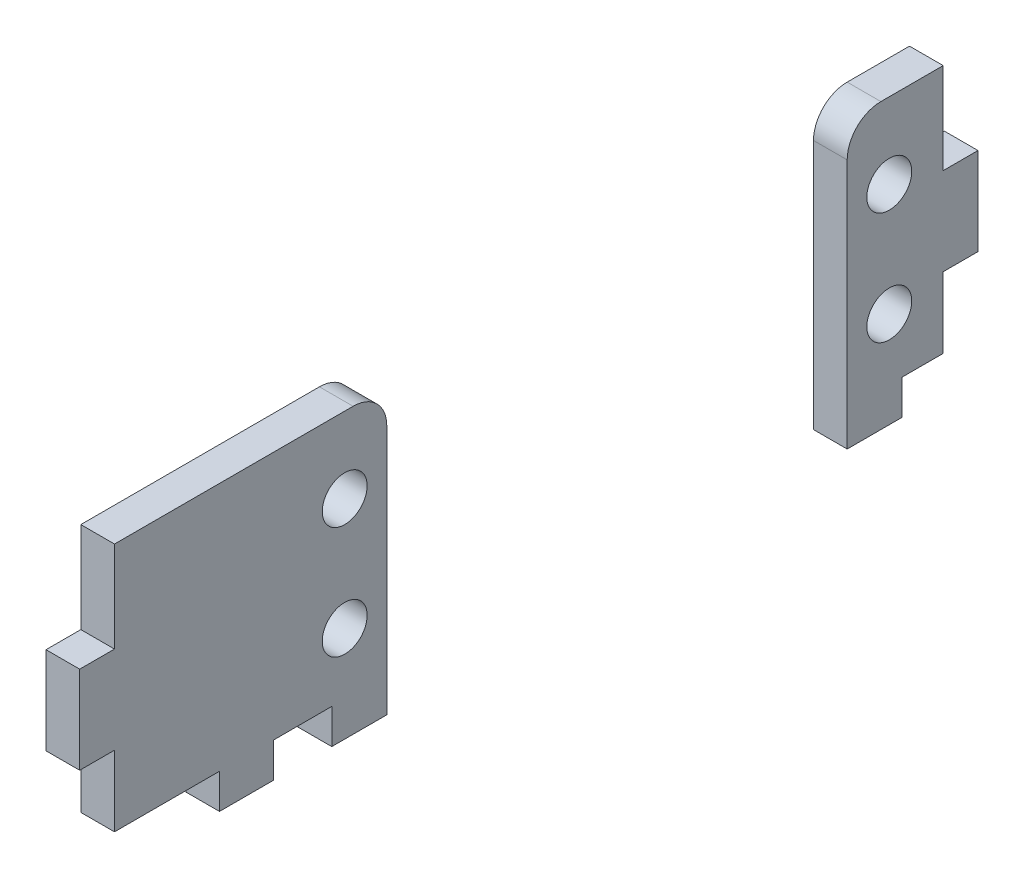
SolidWorks part; units mm, degrees
ref_plane "Front Plane" through (0, 0, 0) normal (0, 0, 1) x (1, 0, 0)
ref_plane "Top Plane" through (0, 0, 0) normal (0, 1, 0) x (1, 0, 0)
ref_plane "Right Plane" through (0, 0, 0) normal (1, 0, 0) x (0, 0, -1)
sketch "Sketch1" plane through (0, 0, 0) normal (1, 0, 0) x (0, 0, -1)
  line L0 (27.35, 0) -> (27.35, -25.3)
  line L1 (0, 0) -> (80, 0) construction
  line L2 (0, 0) -> (0, -25.3)
  line L3 (0, -25.3) -> (80, -25.3) construction
  line L4 (80, 0) -> (80, -25.3)
  line L5 (68.35, 0) -> (68.35, -25.3)
  line L6 (27.35, 0) -> (27.35, -22.3) construction
  line L7 (68.35, 0) -> (68.35, -22.3) construction
  line L8 (0, 0) -> (27.35, 0)
  line L9 (68.35, 0) -> (80, 0)
  line L10 (80, -25.3) -> (68.35, -25.3)
  line L11 (27.35, -25.3) -> (0, -25.3)
  circle A0 centre (23.6, -6.75) radius 3.8 construction
  circle A1 centre (23.6, -6.75) radius 2 construction
  circle A2 centre (72.1, -6.75) radius 3.8 construction
  circle A3 centre (72.1, -6.75) radius 2 construction
  circle A4 centre (72.1, -16.75) radius 2 construction
  circle A5 centre (72.1, -16.75) radius 3.8 construction
  circle A6 centre (23.6, -16.75) radius 3.8 construction
  circle A7 centre (23.6, -16.75) radius 2 construction
  circle A8 centre (23.6, -6.75) radius 3.8 construction
  circle A9 centre (23.6, -6.75) radius 2
  circle A10 centre (72.1, -6.75) radius 3.8 construction
  circle A11 centre (72.1, -6.75) radius 2
  circle A12 centre (72.1, -16.75) radius 2
  circle A13 centre (72.1, -16.75) radius 3.8 construction
  circle A14 centre (23.6, -16.75) radius 3.8 construction
  circle A15 centre (23.6, -16.75) radius 2
sketch "Sketch2" plane through (0, 0, 0) normal (0, 0, 1) x (1, 0, 0)
  line L0 (12.3, -40.925) -> (15.3, -40.925) construction
  line L1 (-3, 0) -> (0, 0)
  line L2 (-3, 0) -> (-3, -25.3)
  line L3 (-3, -25.3) -> (0, -25.3)
  line L4 (0, 0) -> (0, -25.3)
extrude "Boss-Extrude1" add sketch "Sketch1" against normal up to vertex (3 mm away) up to point (-3, 0, 0)
sketch "Sketch3" plane through (0, 0, 0) normal (1, 0, 0) x (0, 0, -1)
  line L4 (17.35, -22.3) -> (17.35, -25.3)
  line L5 (17.35, -25.3) -> (22.35, -25.3)
  line L6 (22.35, -25.3) -> (22.35, -22.3)
  line L7 (22.35, -22.3) -> (17.35, -22.3)
  line L8 (17.35, -22.3) -> (17.35, -25.3) construction
  line L9 (17.35, -25.3) -> (22.35, -25.3) construction
  line L10 (22.35, -25.3) -> (22.35, -22.3) construction
  line L11 (22.35, -22.3) -> (17.35, -22.3) construction
  line L12 (77, 0) -> (77, -8)
  line L13 (80, 0) -> (77, 0)
  line L14 (80, -8) -> (80, 0)
  line L15 (77, -8) -> (80, -8)
  line L16 (77, 0) -> (77, -8) construction
  line L17 (80, 0) -> (77, 0) construction
  line L18 (80, -8) -> (80, 0) construction
  line L19 (77, -8) -> (80, -8) construction
  line L20 (3, -8) -> (3, 0)
  line L21 (3, 0) -> (0, 0)
  line L22 (0, 0) -> (0, -8)
  line L23 (0, -8) -> (3, -8)
  line L24 (3, -8) -> (3, 0) construction
  line L25 (3, 0) -> (0, 0) construction
  line L26 (0, 0) -> (0, -8) construction
  line L27 (0, -8) -> (3, -8) construction
  line L30 (77, -16) -> (77, -22.3)
  line L31 (80, -16) -> (77, -16)
  line L32 (80, -25.3) -> (80, -16)
  line L33 (73.35, -25.3) -> (80, -25.3)
  line L34 (73.35, -22.3) -> (73.35, -25.3)
  line L35 (77, -22.3) -> (73.35, -22.3)
  line L36 (77, -16) -> (77, -22.3) construction
  line L37 (80, -16) -> (77, -16) construction
  line L38 (80, -25.3) -> (80, -16) construction
  line L39 (73.35, -25.3) -> (80, -25.3) construction
  line L40 (73.35, -22.3) -> (73.35, -25.3) construction
  line L41 (77, -22.3) -> (73.35, -22.3) construction
  line L42 (12.35, -22.3) -> (3, -22.3)
  line L43 (12.35, -25.3) -> (12.35, -22.3)
  line L44 (0, -25.3) -> (12.35, -25.3)
  line L45 (0, -16) -> (0, -25.3)
  line L46 (3, -16) -> (0, -16)
  line L47 (3, -22.3) -> (3, -16)
  line L48 (12.35, -22.3) -> (3, -22.3) construction
  line L49 (12.35, -25.3) -> (12.35, -22.3) construction
  line L50 (0, -25.3) -> (12.35, -25.3) construction
  line L51 (0, -16) -> (0, -25.3) construction
  line L52 (3, -16) -> (0, -16) construction
  line L53 (3, -22.3) -> (3, -16) construction
  line L72 (17.25, -22.2) -> (17.25, -25.4)
  line L73 (17.25, -25.4) -> (22.45, -25.4)
  line L74 (22.45, -25.4) -> (22.45, -22.2)
  line L75 (22.45, -22.2) -> (17.25, -22.2)
  line L76 (76.9, 0.1) -> (76.9, -8.1)
  line L77 (76.9, -8.1) -> (80.1, -8.1)
  line L78 (80.1, -8.1) -> (80.1, 0.1)
  line L79 (80.1, 0.1) -> (76.9, 0.1)
  line L80 (3.1, -8.1) -> (3.1, 0.1)
  line L81 (3.1, 0.1) -> (-0.1, 0.1)
  line L82 (-0.1, 0.1) -> (-0.1, -8.1)
  line L83 (-0.1, -8.1) -> (3.1, -8.1)
  line L84 (76.9, -15.9) -> (76.9, -22.2)
  line L85 (76.9, -22.2) -> (73.25, -22.2)
  line L86 (73.25, -22.2) -> (73.25, -25.4)
  line L87 (73.25, -25.4) -> (80.1, -25.4)
  line L88 (80.1, -25.4) -> (80.1, -15.9)
  line L89 (80.1, -15.9) -> (76.9, -15.9)
  line L90 (12.45, -22.2) -> (3.1, -22.2)
  line L91 (3.1, -22.2) -> (3.1, -15.9)
  line L92 (3.1, -15.9) -> (-0.1, -15.9)
  line L93 (-0.1, -15.9) -> (-0.1, -25.4)
  line L94 (-0.1, -25.4) -> (12.45, -25.4)
  line L95 (12.45, -25.4) -> (12.45, -22.2)
  dimension "D1" = 0
  dimension "D2" = 0
  dimension "D3" = 0
  dimension "D4" = 0
  dimension "D5" = 0
  dimension "D6" = 0.1
extrude "Cut-Extrude1" cut sketch "Sketch3" against normal through all
fillet "Fillet1" radius 3 1 edges at (-1.5, 0, -27.35)
fillet "Fillet2" radius 3 1 edges at (-1.5, 0, -68.35)
